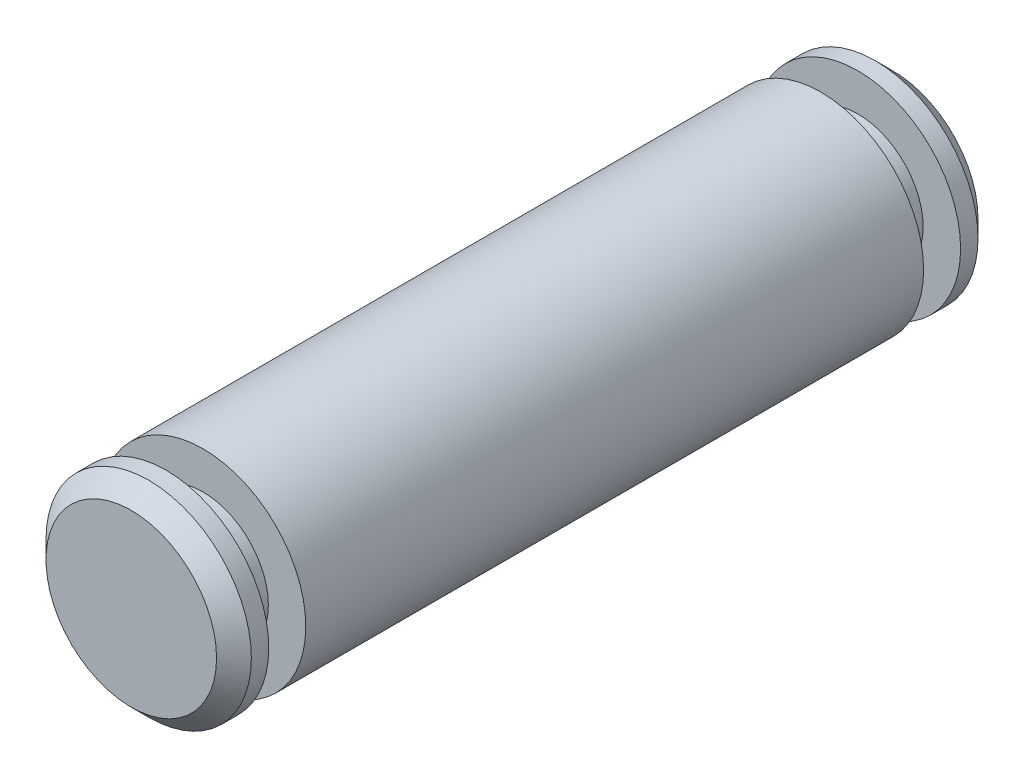
SolidWorks part; units mm, degrees
material "AISI Type A2 Tool Steel"
ref_plane "Front Plane" through (0, 0, 0) normal (0, 0, 1) x (1, 0, 0)
ref_plane "Top Plane" through (0, 0, 0) normal (0, 1, 0) x (1, 0, 0)
ref_plane "Right Plane" through (0, 0, 0) normal (1, 0, 0) x (0, 0, -1)
sketch "Sketch1" plane through (0, 0, 0) normal (0, 0, 1) x (1, 0, 0)
  circle A0 centre (0, 0) radius 1.4986
  dimension "D1" = 2.9972
extrude "Boss-Extrude1" add sketch "Sketch1" along normal mid plane 11.1125
sketch "Sketch2" plane through (0, 0, 0) normal (1, 0, 0) x (0, 0, -1)
  line L0 (-5.5562, -1.4986) -> (5.5562, -1.4986) construction
  line L1 (-5.0482, -1.4986) -> (-4.5083, -1.4986)
  line L2 (-5.0482, -1.4986) -> (-5.0482, -0.9525)
  line L3 (-5.0482, -0.9525) -> (-4.5083, -0.9525)
  line L4 (-4.5083, -1.4986) -> (-4.5083, -0.9525)
  line L5 (-5.5562, 1.4986) -> (-5.5562, -1.4986) construction
  line L6 (-8.828, 0) -> (8.9454, 0) construction
  line L7 (1.6485, 0) -> (-1.6485, 0) construction
  line L8 (0, 2.428) -> (0, -3.7184) construction
  line L9 (4.5083, -1.4986) -> (4.5083, -0.9525)
  line L10 (5.0482, -0.9525) -> (4.5083, -0.9525)
  line L11 (5.0483, -1.4986) -> (5.0482, -0.9525)
  line L12 (5.0483, -1.4986) -> (4.5083, -1.4986)
  point P15 (4.5083, -1.2255)
  dimension "D1" = 0.508
  dimension "D2" = 0.54
  dimension "D3" = 1.905
  dimension "D4" = 9.0165
revolve "Cut-Revolve1" cut sketch "Sketch2" angle 360 about L6
chamfer "Chamfer1" distance 0.254 angle 45
